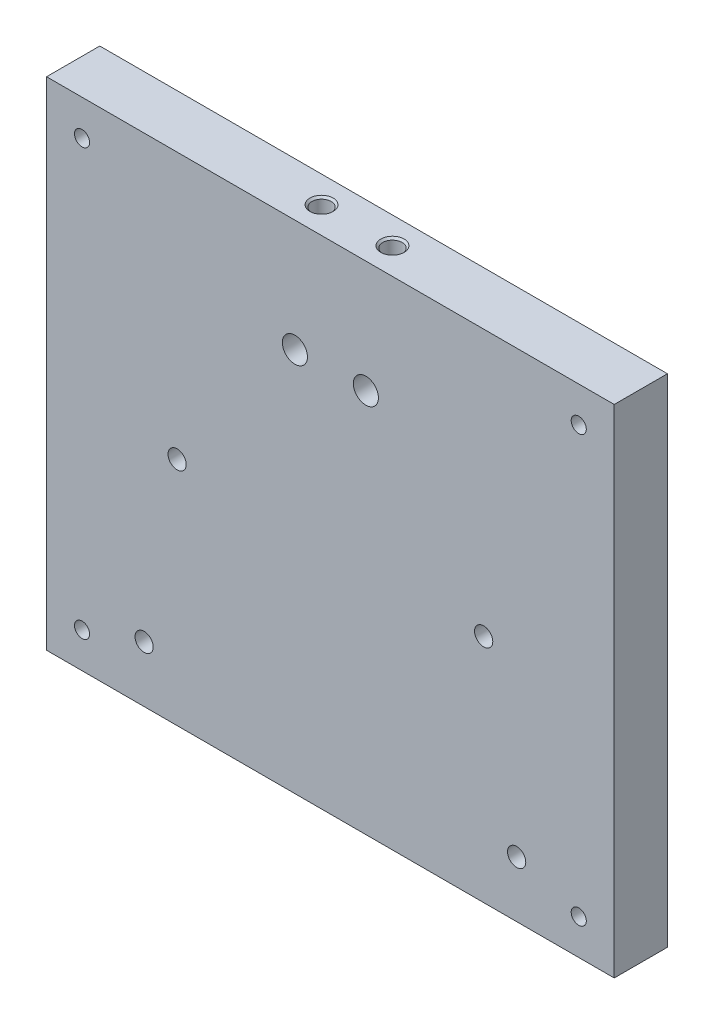
SolidWorks part; units mm, degrees
material "6061-T6 (SS)"
ref_plane "Front Plane" through (0, 0, 0) normal (0, 0, 1) x (1, 0, 0)
ref_plane "Top Plane" through (0, 0, 0) normal (0, 1, 0) x (1, 0, 0)
ref_plane "Right Plane" through (0, 0, 0) normal (1, 0, 0) x (0, 0, -1)
sketch "Sketch1" plane through (0, 0, 0) normal (0, 0, 1) x (1, 0, 0)
  line L1 (0, 0) -> (-101.6, 0)
  line L2 (0, 0) -> (0, 88.9)
  line L3 (0, 88.9) -> (-101.6, 88.9)
  line L4 (-101.6, 0) -> (-101.6, 88.9)
  dimension "D1" = 101.6
  dimension "D2" = 88.9
extrude "Boss-Extrude1" add sketch "Sketch1" along normal blind 9.525
sketch "Sketch5" plane through (0, 88.9, 0) normal (0, 1, 0) x (1, 0, 0)
  line L0 (-101.6, -4.7625) -> (0, -4.7625) construction
  line L1 (-101.6, -9.525) -> (-101.6, 0) construction
  line L2 (0, -9.525) -> (0, 0) construction
  line L3 (-57.15, -4.7625) -> (-44.45, -4.7625)
  point P8 (-50.8, -4.7625)
  dimension "D1" = 12.7
hole_wizard "#8-32 Tapped Hole1" positions "Sketch6" profile "Sketch8" tap size "#8-32" standard "ANSI Inch"
sketch "Sketch6" plane through (0, 88.9, 0) normal (0, 1, 0) x (1, 0, 0)
  point P0 (-44.45, -4.7625)
  point P3 (-57.15, -4.7625)
sketch "Sketch8" plane through (-44.45, 88.9, 4.7625) normal (1, 0, 0) x (0, 0, 1)
  line L0 (0, 0) -> (0, 20.0878)
  line L1 (0, 20.0878) -> (1.7272, 19.05)
  line L2 (1.7272, 19.05) -> (1.7272, 0.3556)
  line L3 (1.7272, 0.3556) -> (2.0828, 0)
  line L5 (2.0828, 0) -> (0, 0)
  line L6 (-1.7272, 0.3556) -> (-2.0828, 0) construction
  line L10 (0, 20.0878) -> (-1.7272, 19.05) construction
  line L11 (0, -6.35) -> (0, 107.95) construction
  dimension "Tap Drill Dia." = 3.4544
  dimension "Tap Drill Depth" = 19.05
  dimension "Near C'Sink Dia." = 4.1656
  dimension "Near C'Sink Angle" = 90
  dimension "Drill Angle" = 118
cosmetic thread "Hole Thread1" parameters "D1"=12.7, "D2"=4.1656
cosmetic thread "Hole Thread2" parameters "D1"=12.7, "D2"=4.1656
hole_wizard "#8 Clearance Hole2" positions "Sketch11" profile "Sketch12" hole size "#8" standard "ANSI Inch"
sketch "Sketch11" plane through (0, 0, 9.525) normal (0, 0, 1) x (1, 0, 0)
  line L0 (-44.45, 68.8122) -> (-42.7228, 69.85) construction
  line L1 (-57.15, 68.8122) -> (-55.4228, 69.85) construction
  line L2 (-44.45, 68.8122) -> (-42.7228, 69.85)
  line L3 (-57.15, 68.8122) -> (-55.4228, 69.85)
  point P1 (-44.45, 68.8122)
  point P3 (-57.15, 68.8122)
sketch "Sketch12" plane through (-44.45, 68.8122, 9.525) normal (1, 0, 0) x (0, -1, 0)
  line L0 (0, 0) -> (0, 26.7507)
  line L1 (0, 26.7507) -> (2.2479, 25.4)
  line L2 (2.2479, 25.4) -> (2.2479, 0)
  line L5 (2.2479, 0) -> (0, 0)
  line L10 (0, 26.7507) -> (-2.2479, 25.4) construction
  line L11 (0, -6.35) -> (0, 107.95) construction
  dimension "Hole Dia." = 4.4958
  dimension "Hole Depth" = 25.4
  dimension "Drill Angle" = 118
sketch "Sketch13" plane through (0, 0, 9.525) normal (0, 0, 1) x (1, 0, 0)
  line L8 (-6.35, 6.35) -> (-6.35, 82.55)
  line L9 (-6.35, 82.55) -> (-95.25, 82.55)
  line L10 (-95.25, 82.55) -> (-95.25, 6.35)
  line L11 (-95.25, 6.35) -> (-6.35, 6.35)
  line L12 (-6.35, 6.35) -> (-6.35, 82.55)
  line L13 (-6.35, 82.55) -> (-95.25, 82.55)
  line L14 (-95.25, 82.55) -> (-95.25, 6.35)
  line L15 (-95.25, 6.35) -> (-6.35, 6.35)
  dimension "D1" = 6.35
hole_wizard "#6-32 Tapped Hole1" positions "Sketch14" profile "Sketch16" tap size "#6-32" standard "ANSI Inch" end condition through all
sketch "Sketch14" plane through (0, 0, 9.525) normal (0, 0, 1) x (1, 0, 0)
  point P0 (-95.25, 6.35)
  point P3 (-95.25, 82.55)
  point P6 (-6.35, 6.35)
  point P9 (-6.35, 82.55)
sketch "Sketch16" plane through (-95.25, 6.35, 9.525) normal (1, 0, 0) x (0, -1, 0)
  line L0 (0, 0) -> (0, 9.525)
  line L1 (0, 9.525) -> (1.3525, 9.525)
  line L2 (1.3525, 9.525) -> (1.3525, 0)
  line L5 (1.3525, 0) -> (0, 0)
  line L11 (0, -6.35) -> (0, 107.95) construction
  dimension "Thru Tap Drill Dia." = 2.7051
  dimension "Thru Tap Drill Depth" = 9.525
cosmetic thread "Hole Thread3" parameters "D2"=3.5052
cosmetic thread "Hole Thread4" parameters "D2"=3.5052
cosmetic thread "Hole Thread5" parameters "D2"=3.5052
cosmetic thread "Hole Thread6" parameters "D2"=3.5052
sketch "Sketch17" plane through (0, 0, 9.525) normal (0, 0, 1) x (1, 0, 0)
  line L0 (-82.55, 12.7) -> (-19.05, 12.7)
  line L1 (-82.55, 12.7) -> (-101.6, 12.7)
  line L2 (-101.6, 88.9) -> (-101.6, 0) construction
  line L3 (-19.05, 12.7) -> (0, 12.7)
  line L4 (0, 0) -> (0, 88.9) construction
  line L5 (-101.6, 0) -> (0, 0) construction
  dimension "D1" = 63.5
  dimension "D2" = 12.7
hole_wizard "#4 Clearance Hole1" positions "Sketch18" profile "Sketch20" hole size "#4" standard "ANSI Inch" end condition up to next
sketch "Sketch18" plane through (0, 0, 9.525) normal (0, 0, 1) x (1, 0, 0)
  point P6 (-17.4625, 10.033)
  point P9 (-84.1375, 10.033)
  point P13 (0, 0)
  point P14 (0, 0)
sketch "Sketch20" plane through (-17.4625, 10.033, 9.525) normal (1, 0, 0) x (0, -1, 0)
  line L0 (0, 0) -> (0, 9.525)
  line L1 (0, 9.525) -> (1.6319, 9.525)
  line L2 (1.6319, 9.525) -> (1.6319, 0)
  line L5 (1.6319, 0) -> (0, 0)
  line L11 (0, -6.35) -> (0, 107.95) construction
  dimension "Thru Hole Dia." = 3.2639
  dimension "Thru Hole Depth" = 9.525
hole_wizard "#4 Clearance Hole2" positions "Sketch21" profile "Sketch22" hole size "#4" standard "ANSI Inch" end condition up to next
sketch "Sketch21" plane through (0, 0, 0) normal (0, 0, -1) x (-1, 0, 0)
  point P0 (23.368, 41.275)
  point P3 (78.232, 41.275)
sketch "Sketch22" plane through (-23.368, 41.275, 0) normal (1, 0, 0) x (0, 1, 0)
  line L0 (0, 0) -> (0, 9.525)
  line L1 (0, 9.525) -> (1.6319, 9.525)
  line L2 (1.6319, 9.525) -> (1.6319, 0)
  line L5 (1.6319, 0) -> (0, 0)
  line L11 (0, -6.35) -> (0, 107.95) construction
  dimension "Thru Hole Dia." = 3.2639
  dimension "Thru Hole Depth" = 9.525
